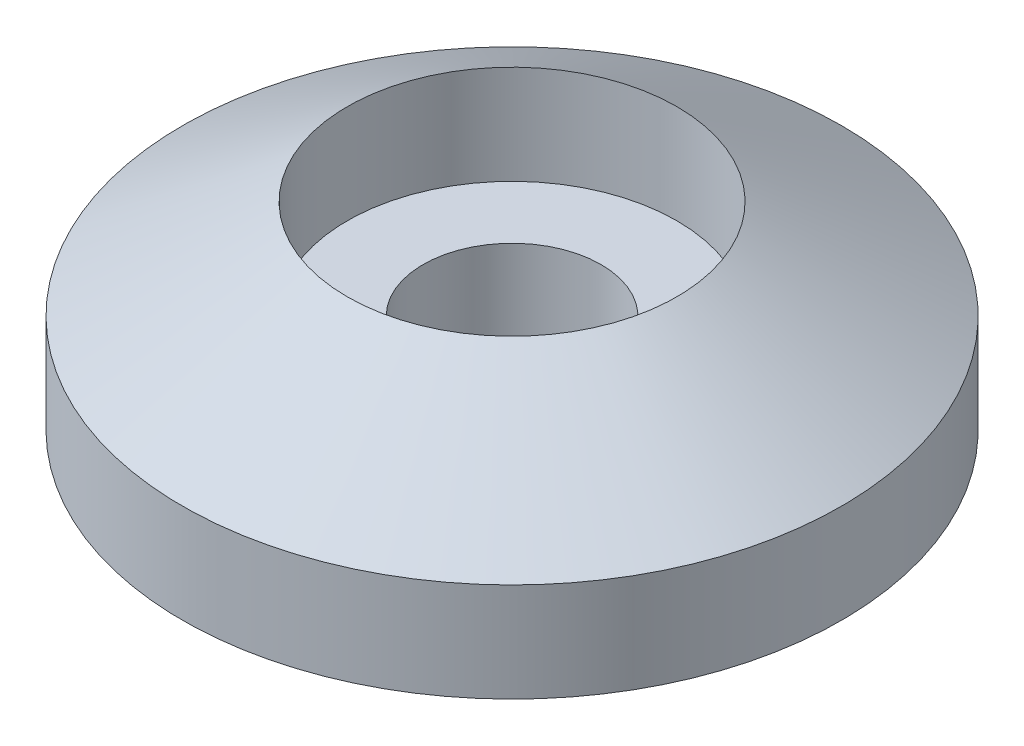
SolidWorks part; units mm, degrees
ref_plane "Front Plane" through (0, 0, 0) normal (0, 0, 1) x (1, 0, 0)
ref_plane "Top Plane" through (0, 0, 0) normal (0, 1, 0) x (1, 0, 0)
ref_plane "Right Plane" through (0, 0, 0) normal (1, 0, 0) x (0, 0, -1)
sketch "Sketch1" plane through (0, 0, 0) normal (0, 0, 1) x (1, 0, 0)
  line L2 (-10, 3) -> (-10, 0)
  line L3 (-10, 0) -> (-2.7, 0)
  line L4 (0, 0) -> (0, 14.5016) construction
  line L5 (-10, 3) -> (-5, 6)
  line L7 (-5, 6) -> (-5, 3)
  line L8 (-5, 3) -> (-2.7, 3)
  line L9 (-2.7, 3) -> (-2.7, 0)
  dimension "D1" = 6
  dimension "D2" = 5
  dimension "D3" = 3
  dimension "D4" = 10
  dimension "D5" = 3
  dimension "D6" = 7.3
revolve "Revolve1" add sketch "Sketch1" angle 360 about L4
